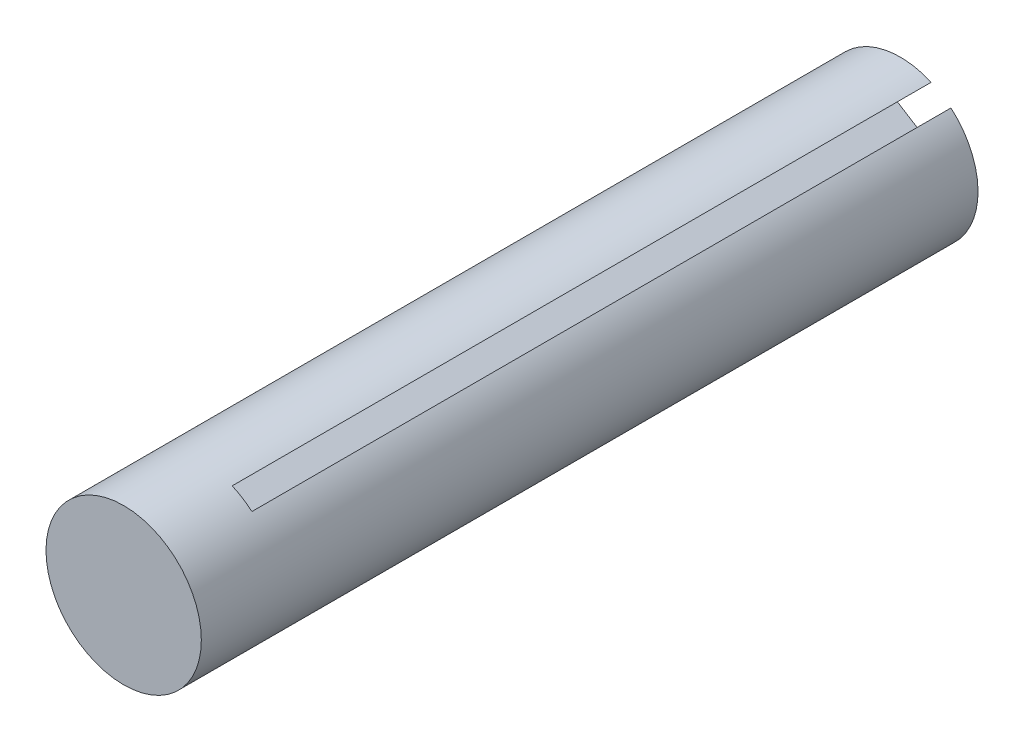
SolidWorks part; units mm, degrees
ref_plane "正面" through (0, 0, 0) normal (0, 0, 1) x (1, 0, 0)
ref_plane "平面" through (0, 0, 0) normal (0, 1, 0) x (1, 0, 0)
ref_plane "右側面" through (0, 0, 0) normal (1, 0, 0) x (0, 0, -1)
sketch "ｽｹｯﾁ1" plane through (0, 0, 0) normal (0, 0, 1) x (1, 0, 0)
  circle A0 centre (-5.3489, 5.1744) radius 10
  dimension "D1" = 20
extrude "ﾎﾞｽ - 押し出し1" add sketch "ｽｹｯﾁ1" along normal blind 100
sketch "ｽｹｯﾁ5" plane through (0, 0, 0) normal (0, 0, -1) x (-1, 0, 0)
  circle A0 centre (5.3489, 5.1744) radius 1.1
  circle A4 centre (5.3489, 5.1744) radius 10 construction
  dimension "D1" = 0
extrude "ｶｯﾄ - 押し出し3" cut sketch "ｽｹｯﾁ5" against normal blind 4
sketch "ｽｹｯﾁ3" plane through (0, 0, 0) normal (0, 0, -1) x (-1, 0, 0)
  line L0 (9.1804, 6.8108) -> (9.2864, 3.8127)
  line L1 (9.1804, 6.8108) -> (9.1274, 8.3099)
  line L2 (9.1274, 8.3099) -> (15.1766, 7.0229)
  line L3 (2.016, 7.6743) -> (4.5595, 9.2652)
  line L4 (2.016, 7.6743) -> (0.7443, 6.8788)
  line L5 (0.7443, 6.8788) -> (-1.1657, 12.7612)
  line L6 (4.5595, 9.2652) -> (5.8312, 10.0606)
  line L7 (5.8312, 10.0606) -> (1.3777, 14.352)
  line L8 (9.2864, 3.8127) -> (9.3394, 2.3136)
  line L9 (1.3777, 14.352) -> (0.3171, 16.0477)
  line L10 (-1.1657, 12.7612) -> (-2.2263, 14.4568)
  line L11 (0.3171, 16.0477) -> (-2.2263, 14.4568)
  line L12 (9.3394, 2.3136) -> (15.2826, 4.0247)
  line L13 (15.2826, 4.0247) -> (17.2814, 4.0954)
  line L14 (15.1766, 7.0229) -> (17.1754, 7.0935)
  line L15 (17.2814, 4.0954) -> (17.1754, 7.0935)
  line L16 (4.8504, 1.0381) -> (2.201, 2.4453)
  line L17 (4.8504, 1.0381) -> (6.1752, 0.3344)
  line L18 (6.1752, 0.3344) -> (2.0359, -4.2609)
  line L19 (2.201, 2.4453) -> (0.8762, 3.1489)
  line L20 (0.8762, 3.1489) -> (-0.6135, -2.8536)
  line L21 (-0.6135, -2.8536) -> (-1.5517, -4.6199)
  line L22 (2.0359, -4.2609) -> (1.0978, -6.0272)
  line L23 (-1.5517, -4.6199) -> (1.0978, -6.0272)
  circle A0 centre (5.3489, 5.1744) radius 10 construction
  circle A3 centre (5.3489, 5.1744) radius 10 construction
  dimension "D1" = 3
  dimension "D2" = 6
  dimension "D3" = 1.5
  dimension "D4" = 120
  dimension "D5" = 3
  dimension "D6" = 8
  dimension "D7" = 1.5
  dimension "D8" = 6
  dimension "D9" = 8
  dimension "D11" = 3
  dimension "D12" = 1.5
  dimension "D13" = 6
  dimension "D14" = 8
  dimension "D15" = 120
extrude "ｶｯﾄ - 押し出し2" cut sketch "ｽｹｯﾁ3" against normal blind 90
